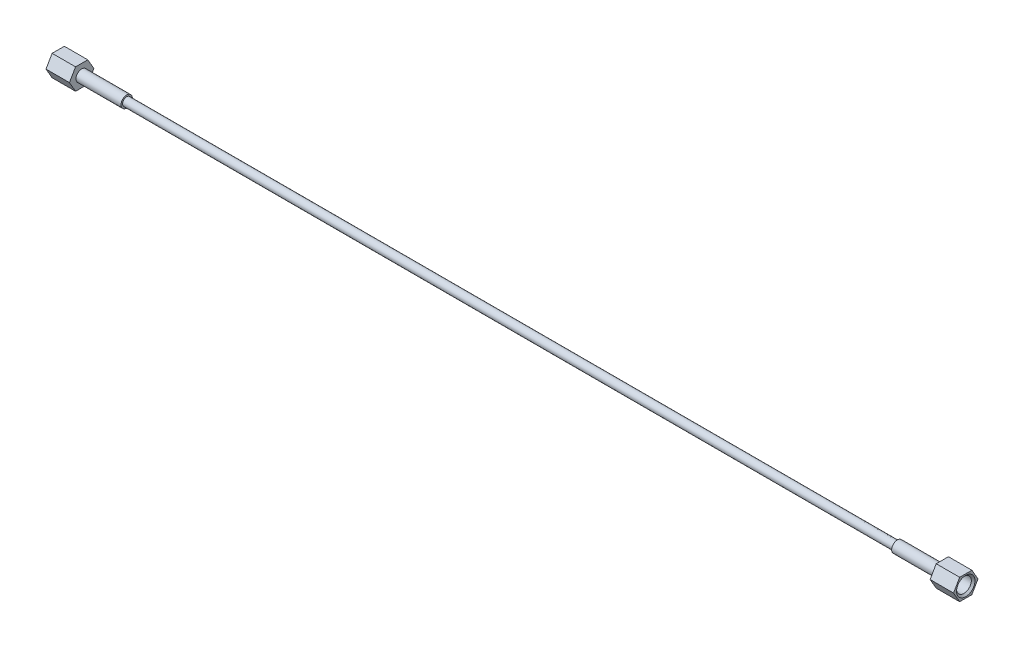
SolidWorks part; units mm, degrees
material "Alloy Steel"
ref_plane "Front Plane" through (0, 0, 0) normal (0, 0, 1) x (1, 0, 0)
ref_plane "Top Plane" through (0, 0, 0) normal (0, 1, 0) x (1, 0, 0)
ref_plane "Right Plane" through (0, 0, 0) normal (1, 0, 0) x (0, 0, -1)
ref_plane "Plane5" through (-6.858, 0, 0) normal (1, 0, 0) x (0, 0, -1)
sketch "Sketch5" plane through (-6.858, 0, 0) normal (1, 0, 0) x (0, 0, -1)
  line L0 (4.1061, 7.112) -> (-4.1061, 7.112)
  line L1 (-4.1061, 7.112) -> (-8.2122, 0)
  line L2 (-8.2122, 0) -> (-4.1061, -7.112)
  line L3 (-4.1061, -7.112) -> (4.1061, -7.112)
  line L4 (4.1061, -7.112) -> (8.2122, 0)
  line L5 (8.2122, 0) -> (4.1061, 7.112)
extrude "Extrude2" add sketch "Sketch5" along normal blind 15.748 separate body
hole_wizard "Hole2" positions "Sketch7" profile "Sketch6" legacy end condition up to next
sketch "Sketch7" plane through (8.89, 0, 0) normal (1, 0, 0) x (0, 0, -1)
  point P0 (0, 0)
sketch "Sketch6" plane through (8.89, 0, 0) normal (0, 1, 0) x (0, 0, -1)
  line L0 (0, 0) -> (0, 15.748)
  line L1 (0, 15.748) -> (3.8354, 15.748)
  line L2 (3.8354, 15.748) -> (3.8354, 9.5661)
  line L3 (3.8354, 9.5661) -> (4.9606, 8.89)
  line L4 (4.9606, 8.89) -> (4.9606, 0)
  line L5 (4.9606, 0) -> (0, 0)
  line L6 (0, -6.13) -> (0, 109.2824) construction
  line L7 (-3.8354, 9.5661) -> (-4.9606, 8.89) construction
  line L8 (0, 15.748) -> (-3.8354, 15.748) construction
  dimension "Diameter" = 7.6708
  dimension "Depth" = 15.748
  dimension "C-Drill Diameter" = 9.9212
  dimension "C-Drill Depth" = 8.89
  dimension "C-Drill Angle" = 118
chamfer "Chamfer2" distance 1.2402 angle 45 1 edges at (8.89, 0, -4.9606)
ref_plane "Plane4" through (0, 0, 0) normal (0, 0, -1) x (-1, 0, 0)
sketch "Sketch8" plane through (0, 0, 0) normal (0, 0, -1) x (-1, 0, 0)
  line L0 (0.6914, 3.81) -> (2.3854, 0.9906)
  line L1 (2.3854, 0.9906) -> (589.4346, 0.9906)
  line L2 (554.736, 3.81) -> (591.1286, 3.81)
  line L3 (554.736, 2.7686) -> (554.736, 3.81)
  line L4 (591.1286, 3.81) -> (589.4346, 0.9906)
  line L5 (554.736, 2.7686) -> (37.084, 2.7686)
  line L6 (37.084, 2.7686) -> (37.084, 3.81)
  line L7 (37.084, 3.81) -> (0.6914, 3.81)
  line L8 (0.6914, 0) -> (202.5086, 0) construction
  line L9 (295.91, 24.5048) -> (295.91, -25.5618) construction
  line L10 (6.858, 7.112) -> (6.858, 0) construction
  line L13 (0.6761, 3.8354) -> (0, 4.9606) construction
  dimension "D1" = 304.8
  dimension "D2" = 1.9812
  dimension "D3" = 5.5372
  dimension "D4" = 7.62
  dimension "D6" = 30.226
revolve "Revolve2" add sketch "Sketch8" angle 360 about L8
ref_plane "Plane6" through (-295.91, 0, 0) normal (1, 0, 0) x (0, 0, -1)
mirror "Mirror2" about plane through (-295.91, 0, 0) normal (1, 0, 0) of bodies 118
